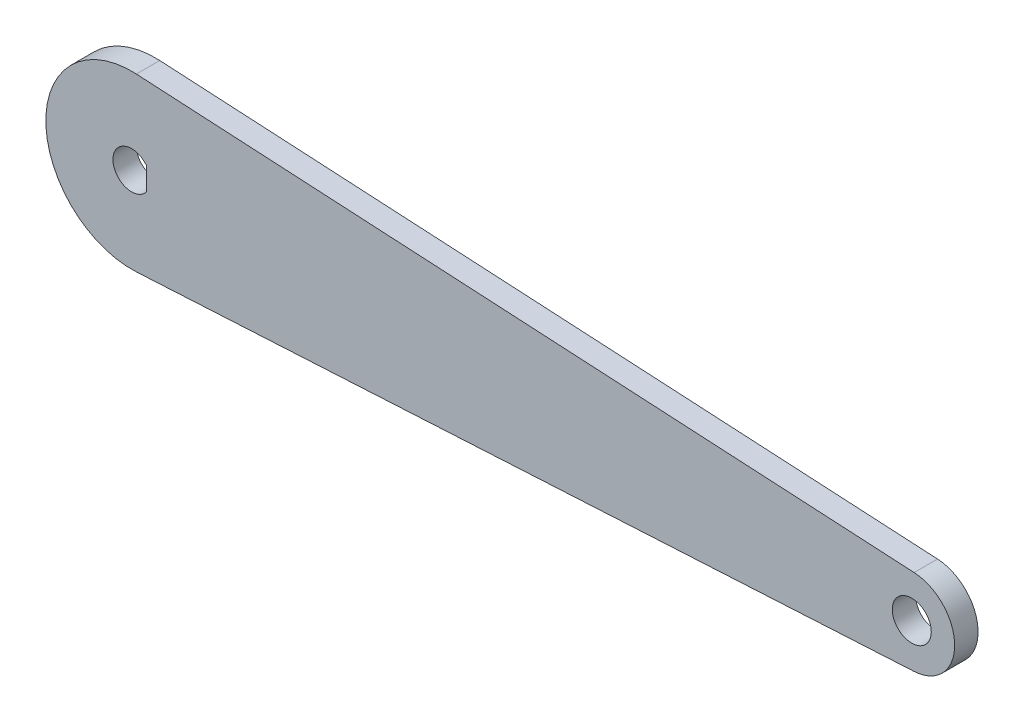
SolidWorks part; units mm, degrees
ref_plane "Front Plane" through (0, 0, 0) normal (0, 0, 1) x (1, 0, 0)
ref_plane "Top Plane" through (0, 0, 0) normal (0, 1, 0) x (1, 0, 0)
ref_plane "Right Plane" through (0, 0, 0) normal (1, 0, 0) x (0, 0, -1)
sketch "Sketch1" plane through (0, 0, 0) normal (0, 0, 1) x (1, 0, 0)
  line L0 (0, 0) -> (100, 0) construction
  line L1 (0.605, 10.9833) -> (100.3025, 5.4917)
  line L2 (0.605, -10.9833) -> (100.3025, -5.4917)
  arc A0 (0.605, 10.9833) -> (0.605, -10.9833) centre (0, 0) ccw
  arc A1 (100.3025, -5.4917) -> (100.3025, 5.4917) centre (100, 0) ccw
  circle A2 centre (100, 0) radius 2.5
  point P3 (50, 0)
  dimension "D1" = 11
  dimension "D2" = 5.5
  dimension "D4" = 5
  dimension "D3" = 100
extrude "Boss-Extrude1" add sketch "Sketch1" along normal blind 3
sketch "Sketch2" plane through (0, 0, 3) normal (0, 0, 1) x (1, 0, 0)
  line L0 (1.9, 1.4663) -> (1.9, -1.4663)
  arc A0 (1.9, 1.4663) -> (1.9, -1.4663) centre (0, 0) ccw
  dimension "D1" = 2.4
  dimension "D2" = 1.9
extrude "Cut-Extrude1" cut sketch "Sketch2" against normal through all
